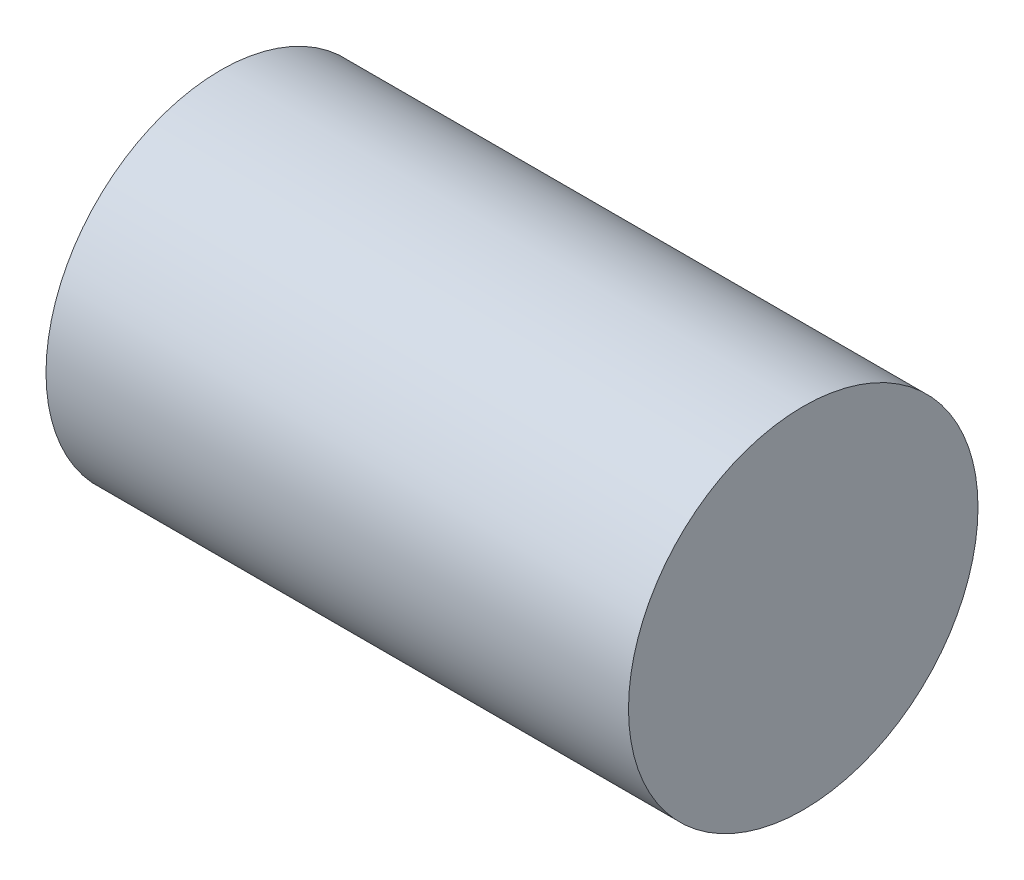
SolidWorks part; units mm, degrees
material "Oak"
ref_plane "Front Plane" through (0, 0, 0) normal (0, 0, 1) x (1, 0, 0)
ref_plane "Top Plane" through (0, 0, 0) normal (0, 1, 0) x (1, 0, 0)
ref_plane "Right Plane" through (0, 0, 0) normal (1, 0, 0) x (0, 0, -1)
sketch "Sketch1" plane through (0, 0, 0) normal (1, 0, 0) x (0, 0, -1)
  circle A0 centre (0, 0) radius 1.5
  dimension "D1" = 3
extrude "Boss-Extrude1" add sketch "Sketch1" along normal blind 5
